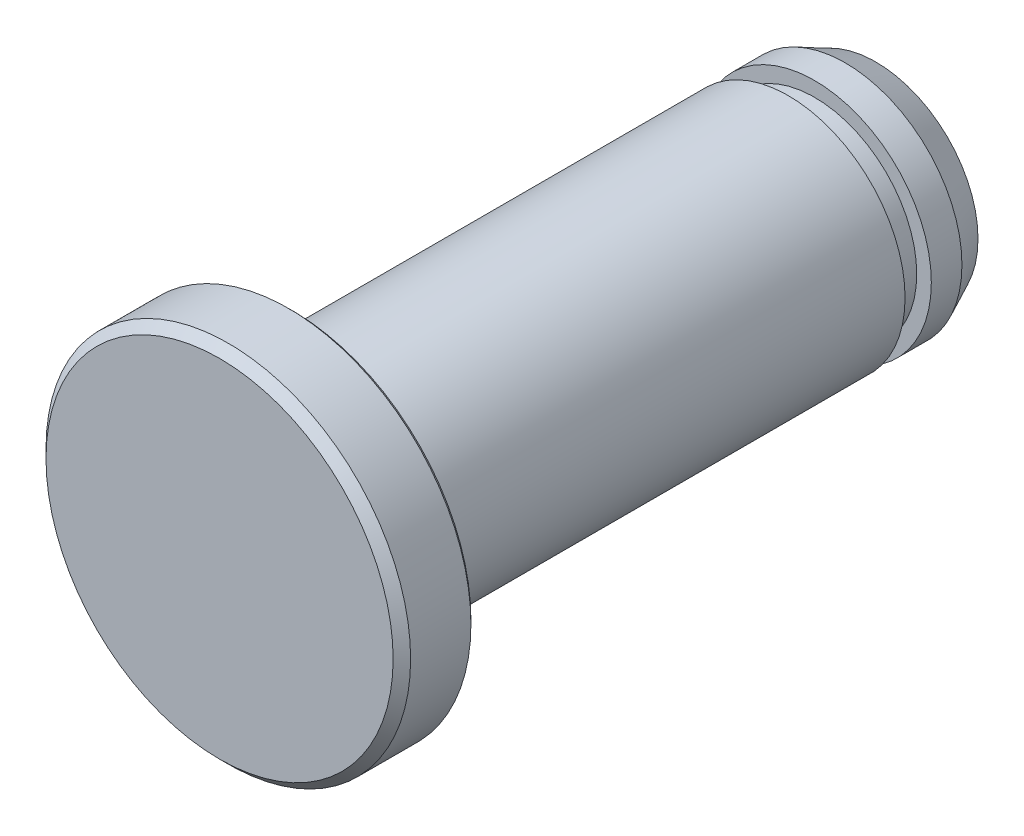
SolidWorks part; units mm, degrees
ref_plane "前视基准面" through (0, 0, 0) normal (0, 0, 1) x (1, 0, 0)
ref_plane "上视基准面" through (0, 0, 0) normal (0, 1, 0) x (1, 0, 0)
ref_plane "右视基准面" through (0, 0, 0) normal (1, 0, 0) x (0, 0, -1)
sketch "草图1" plane through (0, 0, 0) normal (1, 0, 0) x (0, 0, -1)
  line L0 (-12.5, 0) -> (12.5, 0) construction
  line L1 (12.5, 0) -> (15.5, 0)
  line L2 (15.5, 0) -> (15.5, 3.5)
  line L3 (15.5, 3.5) -> (14.45, 4)
  line L4 (14.45, 4) -> (13.4, 4)
  line L5 (13.4, 4) -> (13.4, 3.5)
  line L6 (13.4, 3.5) -> (12.5, 3.5)
  line L7 (12.5, 3.5) -> (12.5, 4)
  line L8 (12.5, 4) -> (0, 4)
  line L9 (0, 4) -> (0, 0)
  line L10 (14.45, 4) -> (15.5, 4) construction
  line L11 (-12.5, 0) -> (-12.5, 6.5)
  line L12 (-12.5, 6.5) -> (-15.2, 6.5)
  line L13 (-15.2, 6.5) -> (-15.5, 6.2)
  line L14 (-15.5, 6.2) -> (-15.5, 0)
  line L15 (-15.5, 0) -> (-12.5, 0)
  dimension "D1" = 45
  dimension "L" = 25
  dimension "Dg6" = 8
  dimension "d" = 7
  dimension "m" = 0.9
  dimension "(M)" = 3
  dimension "H" = 13
  dimension "T" = 3
  dimension "D2" = 0.3
sketch "草图3" plane through (0, 0, 0) normal (1, 0, 0) x (0, 0, -1)
  line L0 (12.5, 0) -> (15.5, 0) construction
  line L1 (15.5, 0) -> (15.5, 3.5) construction
  line L2 (15.5, 3.5) -> (14.45, 4) construction
  line L3 (14.45, 4) -> (13.4, 4) construction
  line L4 (13.4, 4) -> (13.4, 3.5) construction
  line L5 (13.4, 3.5) -> (12.5, 3.5) construction
  line L6 (12.5, 3.5) -> (12.5, 4) construction
  line L7 (12.5, 4) -> (0, 4) construction
  line L9 (12.5, 0) -> (15.5, 0)
  line L10 (15.5, 0) -> (15.5, 3.5)
  line L11 (15.5, 3.5) -> (14.45, 4)
  line L12 (14.45, 4) -> (13.4, 4)
  line L13 (13.4, 4) -> (13.4, 3.5)
  line L14 (13.4, 3.5) -> (12.5, 3.5)
  line L15 (12.5, 3.5) -> (12.5, 4)
  line L16 (12.5, 4) -> (0, 4)
  line L17 (0, 4) -> (-4.3333, 4)
  line L19 (-4.5, 4.1667) -> (-4.5, 6.1167)
  line L20 (-4.6333, 6.25) -> (-6.7, 6.25)
  line L21 (-6.7, 6.25) -> (-7, 5.95)
  line L22 (-7, 5.95) -> (-7, 0)
  line L23 (-7, 0) -> (12.5, 0)
  line L24 (-4.6333, 6.25) -> (-4.5, 6.1167)
  arc A0 (-4.5, 4.1667) -> (-4.3333, 4) centre (-4.3333, 4.1667) ccw
  point P22 (-12.5, 4)
  dimension "D1" = 0.1667
  dimension "D2" = 45
  dimension "D3" = 0.1333
  dimension "D4" = 2.5
  dimension "D5" = 22.5
  dimension "D6" = 0.3
  dimension "D7" = 0.3
  dimension "D8" = 6.25
revolve "旋转1" add sketch "草图3" angle 360 mid plane about L23
